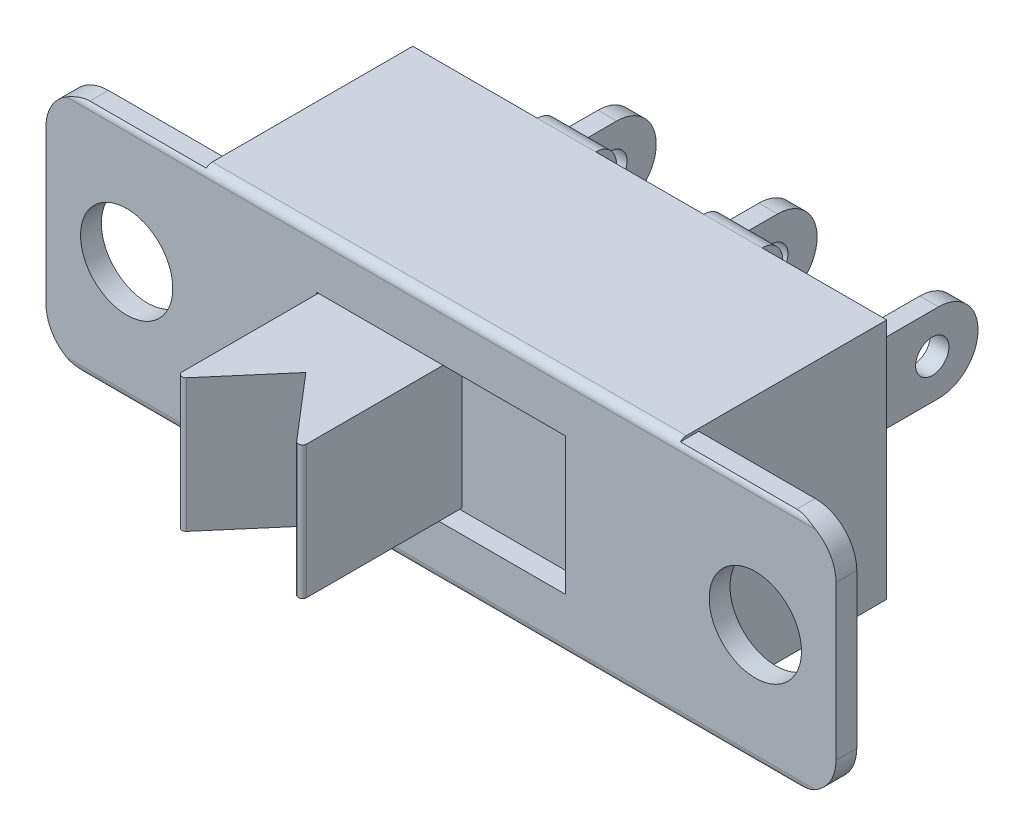
SolidWorks part; units mm, degrees
ref_plane "Face" through (0, 0, 0) normal (0, 0, 1) x (1, 0, 0)
ref_plane "Dessus" through (0, 0, 0) normal (0, 1, 0) x (1, 0, 0)
ref_plane "Droite" through (0, 0, 0) normal (1, 0, 0) x (0, 0, -1)
sketch "Esquisse1" plane through (0, 0, 0) normal (0, 0, 1) x (1, 0, 0)
  line L0 (-11.705, 0) -> (22.0419, 0) construction
  line L1 (0, 14.4412) -> (0, -10.7929) construction
  line L2 (9.5, 14.4412) -> (9.5, -10.7929) construction
  line L3 (-10.9277, 2.85) -> (20.0406, 2.85) construction
  line L4 (-10.9277, -2.85) -> (12.2883, -2.85) construction
  line L5 (-9.5, 7.2304) -> (-9.5, -7.3766) construction
  line L6 (7.56, 6.9447) -> (7.56, -1.85) construction
  line L7 (-8.5, 2.85) -> (8.5, 2.85)
  line L8 (-9.5, 1.85) -> (-9.5, -1.85)
  line L9 (-8.5, -2.85) -> (8.5, -2.85)
  line L10 (9.5, 1.85) -> (9.5, -1.85)
  arc A0 (9.5, 1.85) -> (8.5, 2.85) centre (8.5, 1.85) ccw
  arc A1 (9.5, -1.85) -> (8.5, -2.85) centre (8.5, -1.85) cw
  arc A2 (-8.5, -2.85) -> (-9.5, -1.85) centre (-8.5, -1.85) cw
  arc A3 (-9.5, 1.85) -> (-8.5, 2.85) centre (-8.5, 1.85) cw
  circle A4 centre (7.56, 0) radius 1.11
  circle A5 centre (-7.56, 0) radius 1.11
  dimension "D1" = 1
extrude "Base-Extrusion" add sketch "Esquisse1" along normal blind 0.5
sketch "Esquisse2" plane through (0, 0, 0.5) normal (0, 0, 1) x (1, 0, 0)
  line L0 (5.7, 4.1924) -> (5.7, -5.2261) construction
  line L1 (-5.7, 3.9397) -> (-5.7, -5.4558) construction
  line L2 (-7.5233, 2.91) -> (6.8571, 2.91) construction
  line L3 (-6.7422, -2.91) -> (8.4881, -2.91) construction
  line L5 (-5.7, 2.91) -> (5.7, 2.91)
  line L6 (-5.7, 2.91) -> (-5.7, -2.91)
  line L7 (-5.7, -2.91) -> (5.7, -2.91)
  line L8 (5.7, 2.91) -> (5.7, -2.91)
extrude "Boss.-Extru.1" add sketch "Esquisse2" against normal blind 5.02
sketch "Esquisse3" plane through (0, 0, 0.5) normal (0, 0, 1) x (1, 0, 0)
  line L0 (-5.2491, 1.65) -> (5.8004, 1.65) construction
  line L1 (-5.9152, 0) -> (6.2828, 0) construction
  line L2 (0, 3.664) -> (0, -4.6288) construction
  line L3 (3, 3.9167) -> (3, -2.2168) construction
  line L4 (-3, 3.4573) -> (-3, -2.2168) construction
  line L5 (-3, -1.65) -> (-3, 1.65)
  line L6 (-3, 1.65) -> (3, 1.65)
  line L7 (3, 1.65) -> (3, -1.65)
  line L8 (-3, -1.65) -> (3, -1.65)
  point P15 (3, 0)
  point P16 (-3, 0)
extrude "Enlèv. mat.-Extru.1" cut sketch "Esquisse3" against normal blind 0.5
sketch "Esquisse4" plane through (0, 0, 0) normal (0, 0, 1) x (1, 0, 0)
  line L0 (-4.2383, 1.6) -> (4.7437, 1.6) construction
  line L1 (-4.2383, 0) -> (3.8937, 0) construction
  line L2 (3, -1.0912) -> (3, 3.2046) construction
  line L3 (-3, -3.4343) -> (-3, 3.4343) construction
  line L4 (0, 2.3546) -> (0, -2.4695) construction
  line L5 (-3.8708, -1.6) -> (4.7437, -1.6) construction
  line L7 (-3, 1.6) -> (0, 1.6)
  line L8 (-3, 1.6) -> (-3, -1.6)
  line L9 (-3, -1.6) -> (0, -1.6)
  line L10 (0, 1.6) -> (0, -1.6)
extrude "Boss.-Extru.2" add sketch "Esquisse4" along normal blind 4
sketch "Esquisse5" plane through (0, -1.6, 0) normal (0, -1, 0) x (1, 0, 0)
  line L0 (-5.1281, 4) -> (5.1876, 4) construction
  line L1 (0, 6.1167) -> (0, -6.3394) construction
  line L2 (-3, 2.25) -> (-3, 9.5652) construction
  line L3 (-1.5, 7.2761) -> (-1.5, -6.3394) construction
  line L4 (1.531, 2.25) -> (-5.1281, 2.25) construction
  line L5 (0, 4) -> (-1.5, 2.25)
  line L6 (-1.5, 2.25) -> (-3, 4)
  line L7 (-3, 4) -> (-3, 5.0465)
  line L8 (-3, 5.0465) -> (0, 5.0465)
  line L9 (0, 5.0465) -> (0, 4)
extrude "Enlèv. mat.-Extru.2" cut sketch "Esquisse5" against normal through all
fillet "Congé1" radius 0.1
sketch "Esquisse6" plane through (0, 0, -4.52) normal (0, 0, -1) x (-1, 0, 0)
  line L0 (0, 4.1464) -> (0, -6.3517) construction
  line L1 (3.87, 3.9626) -> (3.87, -5.1572) construction
  line L2 (-4.6288, 0.955) -> (4.8585, 0.955) construction
  line L3 (-4.6288, -0.955) -> (4.5369, -0.955) construction
  line L4 (0.225, 1.1359) -> (0.225, -1.5505) construction
  line L5 (-0.225, 0.955) -> (0.225, 0.955)
  line L6 (-0.225, 0.955) -> (-0.225, -0.955)
  line L7 (0.225, 0.955) -> (0.225, -0.955)
  line L8 (-0.225, -0.955) -> (0.225, -0.955)
  line L9 (3.645, 0.955) -> (3.645, -0.955)
  line L10 (4.095, 0.955) -> (4.095, -0.955)
  line L11 (3.645, -0.955) -> (4.095, -0.955)
  line L12 (3.645, 0.955) -> (4.095, 0.955)
  line L13 (-3.645, 0.955) -> (-4.095, 0.955)
  line L14 (-3.645, -0.955) -> (-4.095, -0.955)
  line L15 (-4.095, 0.955) -> (-4.095, -0.955)
  line L16 (-3.645, 0.955) -> (-3.645, -0.955)
extrude "Boss.-Extru.3" add sketch "Esquisse6" along normal blind 3.8
fillet "Congé2" radius 0.95
sketch "Esquisse7" plane through (4.095, 0, 0) normal (1, 0, 0) x (0, 0, -1)
  line L0 (7.22, 0.8593) -> (7.22, -4.0029) construction
  line L1 (0.4163, 0) -> (8.804, 0) construction
  circle A0 centre (7.22, 0) radius 0.4
extrude "Enlèv. mat.-Extru.3" cut sketch "Esquisse7" against normal through all
sketch "Esquisse8" plane through (0, 0, -4.52) normal (0, 0, -1) x (-1, 0, 0)
  line L0 (0, 3.9856) -> (0, -5.1572) construction
  line L1 (-10.211, 0) -> (10.3029, 0) construction
  line L2 (-5.4099, 1.51) -> (7.5692, 1.51) construction
  line L3 (1.3, 3.5032) -> (1.3, -2.1708) construction
  line L4 (2.7, 3.5032) -> (2.7, -0.9763) construction
  line L5 (3.2298, 2.91) -> (0.7595, 2.91) construction
  line L6 (1.3, -1.51) -> (2.7, -1.51)
  line L7 (1.3, 2.91) -> (2.7, 2.91)
  line L8 (1.3, 2.91) -> (1.3, 1.51)
  line L9 (1.3, 1.51) -> (2.7, 1.51)
  line L10 (2.7, 2.91) -> (2.7, 1.51)
  line L11 (1.3, -2.91) -> (1.3, -1.51)
  line L12 (2.7, -2.91) -> (2.7, -1.51)
  line L13 (1.3, -2.91) -> (2.7, -2.91)
  line L14 (-2.7, 2.91) -> (-2.7, 1.51)
  line L15 (-1.3, 2.91) -> (-2.7, 2.91)
  line L16 (-1.3, 2.91) -> (-1.3, 1.51)
  line L17 (-1.3, 1.51) -> (-2.7, 1.51)
  line L18 (-1.3, -1.51) -> (-2.7, -1.51)
  line L19 (-2.7, -2.91) -> (-2.7, -1.51)
  line L20 (-1.3, -2.91) -> (-2.7, -2.91)
  line L21 (-1.3, -2.91) -> (-1.3, -1.51)
extrude "Boss.-Extru.4" add sketch "Esquisse8" along normal blind 0.5
fillet "Congé3" radius 0.5
fillet "Congé4" radius 0.2
